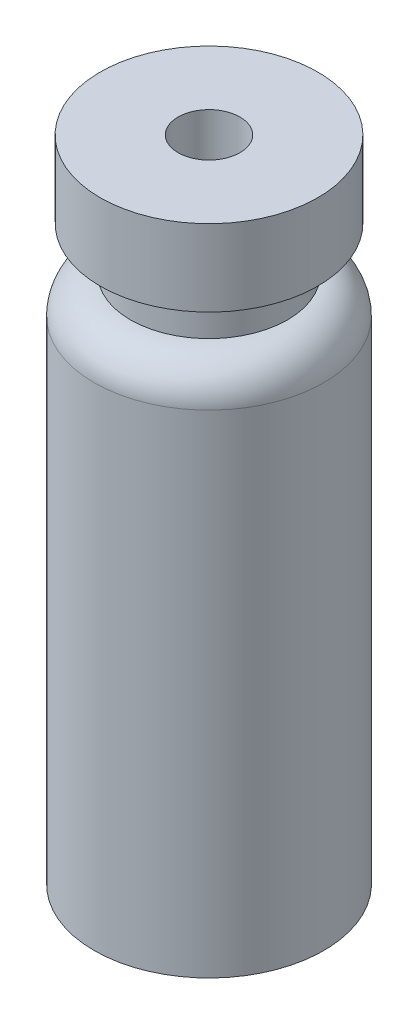
SolidWorks part; units mm, degrees
ref_plane "Front Plane" through (0, 0, 0) normal (0, 0, 1) x (1, 0, 0)
ref_plane "Top Plane" through (0, 0, 0) normal (0, 1, 0) x (1, 0, 0)
ref_plane "Right Plane" through (0, 0, 0) normal (1, 0, 0) x (0, 0, -1)
sketch "Sketch2" plane through (0, 0, 0) normal (0, 0, 1) x (1, 0, 0)
  line L0 (0, 32.2) -> (0, 0) construction
  line L1 (0, 0) -> (5.7, 0)
  line L2 (5.7, 0) -> (5.7, 24.4)
  line L3 (3.9, 26.2) -> (3.9, 28.4)
  line L4 (3.9, 28.4) -> (5.4, 28.4)
  line L5 (5.4, 28.4) -> (5.4, 32.2)
  line L6 (5.4, 32.2) -> (1.535, 32.2)
  line L7 (1.535, 32.2) -> (1.535, 9.8342)
  line L8 (1.535, 9.8342) -> (0.4935, 3.4199)
  line L9 (0, 3) -> (0, 0)
  arc A0 (5.7, 24.4) -> (3.9, 26.2) centre (3.9, 24.4) ccw
  arc A1 (0.4935, 3.4199) -> (0, 3) centre (0, 3.5) cw
  dimension "D8" = 0.5
  dimension "D1" = 5.7
  dimension "D2" = 24.4
  dimension "D3" = 3.8
  dimension "D4" = 4
  dimension "D5" = 5.4
  dimension "D6" = 3.07
  dimension "D7" = 3.9
  dimension "D9" = 3
revolve "Revolve1" add sketch "Sketch2" angle 360 about L0
